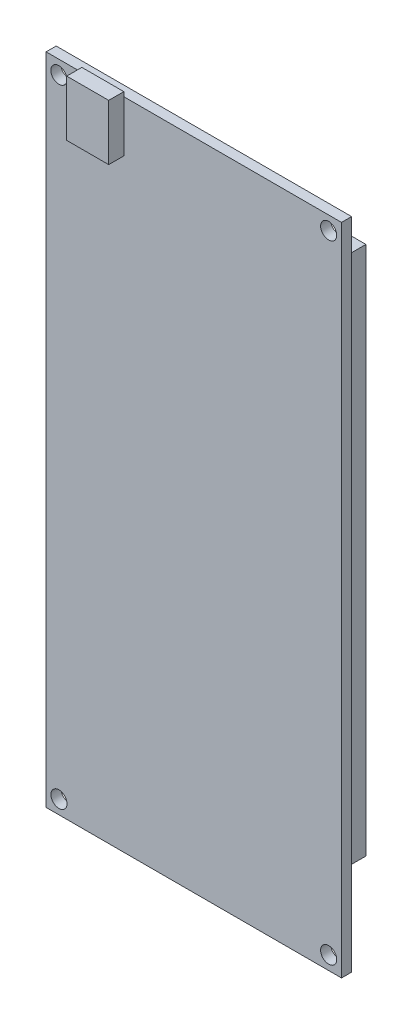
SolidWorks part; units mm, degrees
ref_plane "Front Plane" through (0, 0, 0) normal (0, 0, 1) x (1, 0, 0)
ref_plane "Top Plane" through (0, 0, 0) normal (0, 1, 0) x (1, 0, 0)
ref_plane "Right Plane" through (0, 0, 0) normal (1, 0, 0) x (0, 0, -1)
sketch "Sketch1" plane through (0, 0, 0) normal (0, 0, 1) x (1, 0, 0)
  line L1 (29.3, -64.9) -> (-29.3, -64.9)
  line L2 (29.3, -64.9) -> (29.3, 64.9)
  line L3 (29.3, 64.9) -> (-29.3, 64.9)
  line L4 (-29.3, -64.9) -> (-29.3, 64.9)
  line L5 (29.3, -64.9) -> (-29.3, 64.9) construction
  line L6 (29.3, 64.9) -> (-29.3, -64.9) construction
  line L7 (26.75, 62.2) -> (-26.75, 62.2) construction
  line L8 (26.75, 62.2) -> (26.75, -62.2) construction
  line L9 (26.75, -62.2) -> (-26.75, -62.2) construction
  line L10 (-26.75, 62.2) -> (-26.75, -62.2) construction
  line L11 (26.75, 62.2) -> (-26.75, -62.2) construction
  line L12 (26.75, -62.2) -> (-26.75, 62.2) construction
  circle A0 centre (-26.75, 62.2) radius 1.6
  circle A1 centre (26.75, 62.2) radius 1.6
  circle A2 centre (-26.75, -62.2) radius 1.6
  circle A3 centre (26.75, -62.2) radius 1.6
  point P0 (0, 0)
  point P6 (0, 0)
  dimension "D1" = 3.2
  dimension "D2" = 53.5
  dimension "D3" = 124.4
  dimension "D4" = 129.8
  dimension "D5" = 58.6
extrude "Boss-Extrude1" add sketch "Sketch1" along normal blind 2
sketch "Sketch2" plane through (0, 0, 0) normal (0, 0, -1) x (-1, 0, 0)
  line L1 (-23.1379, 52.5401) -> (-18.8416, 52.5401)
  line L2 (-23.1379, 52.5401) -> (-23.1379, -52.5401)
  line L3 (-23.1379, -52.5401) -> (-18.8416, -52.5401)
  line L4 (-18.8416, 52.5401) -> (-18.8416, -52.5401)
  line L5 (-23.1379, 52.5401) -> (-18.8416, -52.5401) construction
  line L6 (-23.1379, -52.5401) -> (-18.8416, 52.5401) construction
  line L7 (23.7633, 52.5401) -> (19.8251, 52.5401)
  line L8 (23.7633, 52.5401) -> (23.7633, -52.5401)
  line L9 (23.7633, -52.5401) -> (19.8251, -52.5401)
  line L10 (19.8251, 52.5401) -> (19.8251, -52.5401)
  line L11 (23.7633, 52.5401) -> (19.8251, -52.5401) construction
  line L12 (23.7633, -52.5401) -> (19.8251, 52.5401) construction
  point P0 (-20.9898, 0)
  point P5 (21.7942, 0)
extrude "Boss-Extrude2" add sketch "Sketch2" along normal offset from surface (9 mm away) 11 up to face at (-25.15, -62.2, 2)
sketch "Sketch3" plane through (0, 0, 2) normal (0, 0, 1) x (1, 0, 0)
  line L1 (-22.2051, 54.731) -> (-13.8794, 54.731)
  line L2 (-22.2051, 54.731) -> (-22.2051, 65.7754)
  line L3 (-22.2051, 65.7754) -> (-13.8794, 65.7754)
  line L4 (-13.8794, 54.731) -> (-13.8794, 65.7754)
  line L5 (-22.2051, 54.731) -> (-13.8794, 65.7754) construction
  line L6 (-22.2051, 65.7754) -> (-13.8794, 54.731) construction
  point P0 (-18.0422, 60.2532)
  point P5 (-18.0422, 60.2532)
extrude "Boss-Extrude3" add sketch "Sketch3" along normal blind 3
